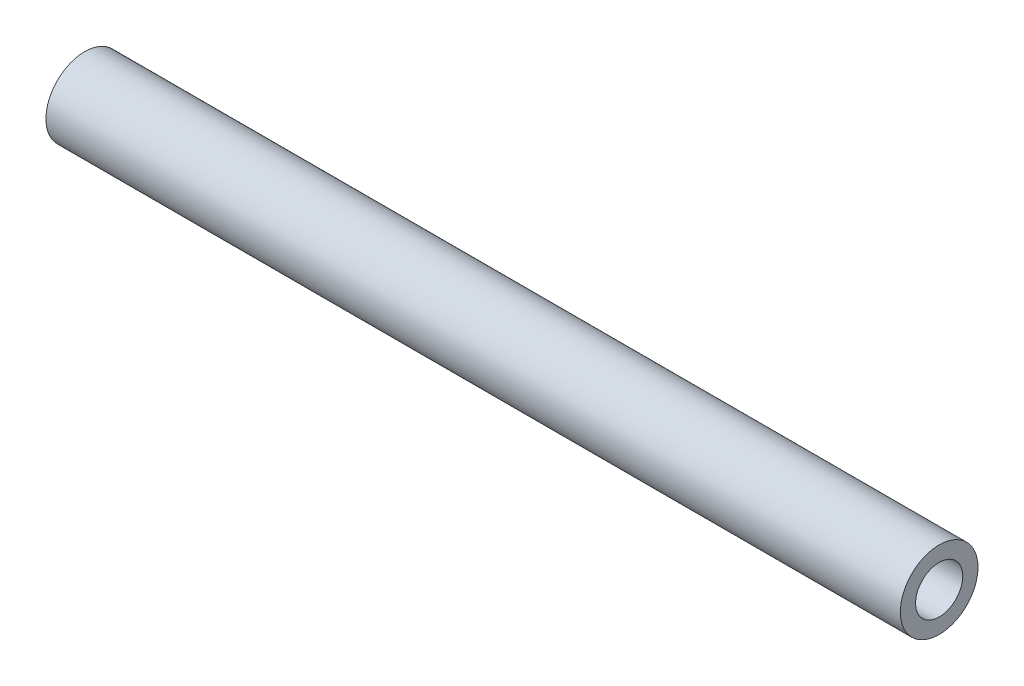
SolidWorks part; units mm, degrees
material "6061-T6 (SS)"
ref_plane "Front" through (0, 0, 0) normal (0, 0, 1) x (1, 0, 0)
ref_plane "Top" through (0, 0, 0) normal (0, 1, 0) x (1, 0, 0)
ref_plane "Right" through (0, 0, 0) normal (1, 0, 0) x (0, 0, -1)
sketch "Sketch1" plane through (0, 0, 0) normal (1, 0, 0) x (0, 0, -1)
  circle A0 centre (0, 0) radius 1.9304
  circle A1 centre (0, 0) radius 3.175
  dimension "D1" = 1.2446
  dimension "D2" = 6.35
extrude "Boss-Extrude1" add sketch "Sketch1" along normal mid plane 69.85
